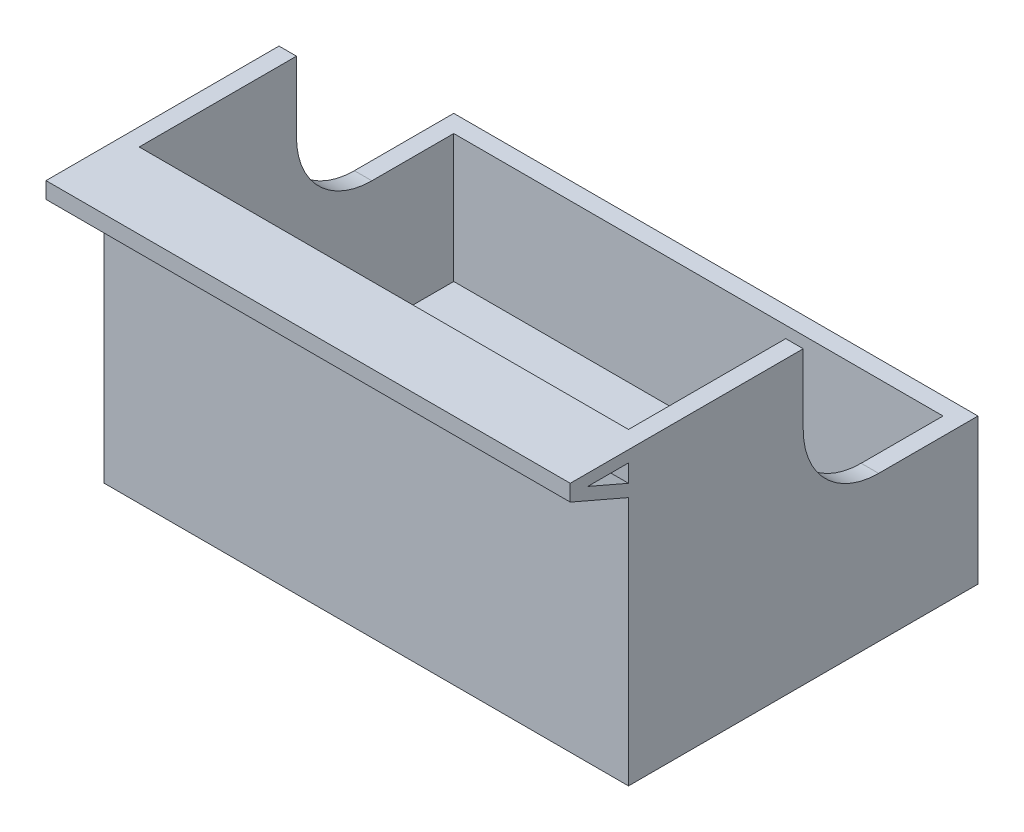
SolidWorks part; units mm, degrees
ref_plane "Front Plane" through (0, 0, 0) normal (0, 0, 1) x (1, 0, 0)
ref_plane "Top Plane" through (0, 0, 0) normal (0, 1, 0) x (1, 0, 0)
ref_plane "Right Plane" through (0, 0, 0) normal (1, 0, 0) x (0, 0, -1)
sketch "Sketch1" plane through (0, 0, 0) normal (0, 1, 0) x (1, 0, 0)
  line L1 (45, -30) -> (-45, -30)
  line L2 (45, -30) -> (45, 30)
  line L3 (45, 30) -> (-45, 30)
  line L4 (-45, -30) -> (-45, 30)
  line L5 (45, -30) -> (-45, 30) construction
  line L6 (45, 30) -> (-45, -30) construction
  point P0 (0, 0)
  dimension "D1" = 60
  dimension "D2" = 90
extrude "Boss-Extrude1" add sketch "Sketch1" along normal blind 50
shell "Shell1" thickness 3
sketch "Sketch2" plane through (-45, 0, 0) normal (-1, 0, 0) x (0, 0, 1)
  line L0 (-30, 25) -> (31.3438, 25) construction
  line L1 (-30, 50) -> (-30, 0) construction
  line L2 (0, 50) -> (0, -2.717) construction
  line L3 (-30, 50) -> (30, 50) construction
  line L4 (-30, 25) -> (-12.9435, 25)
  line L5 (0, 37.9435) -> (0, 50)
  line L6 (-30, 25) -> (-30, 50)
  line L7 (-30, 50) -> (0, 50)
  arc A0 (-12.9435, 25) -> (0, 37.9435) centre (-12.9435, 37.9435) ccw
extrude "Cut-Extrude1" cut sketch "Sketch2" against normal up to surface (90 mm away) up to face at (45, 25, 0)
sketch "Sketch3" plane through (-45, 0, 0) normal (-1, 0, 0) x (0, 0, 1)
  line L0 (30, 50) -> (40, 50)
  line L1 (40, 50) -> (40, 47.1977)
  line L2 (40, 47.1977) -> (30, 42.868)
  line L3 (30, 50) -> (30, 0) construction
  line L4 (30, 42.868) -> (30, 44.9975)
  line L5 (30, 44.9975) -> (37, 48.0283)
  line L6 (37, 48.0283) -> (30, 48.0283)
  line L7 (30, 48.0283) -> (30, 50)
  dimension "D1" = 10
  dimension "D2" = 7
extrude "Boss-Extrude2" add sketch "Sketch3" against normal up to surface (90 mm away) up to face at (45, 26.4661, -1.4661)
